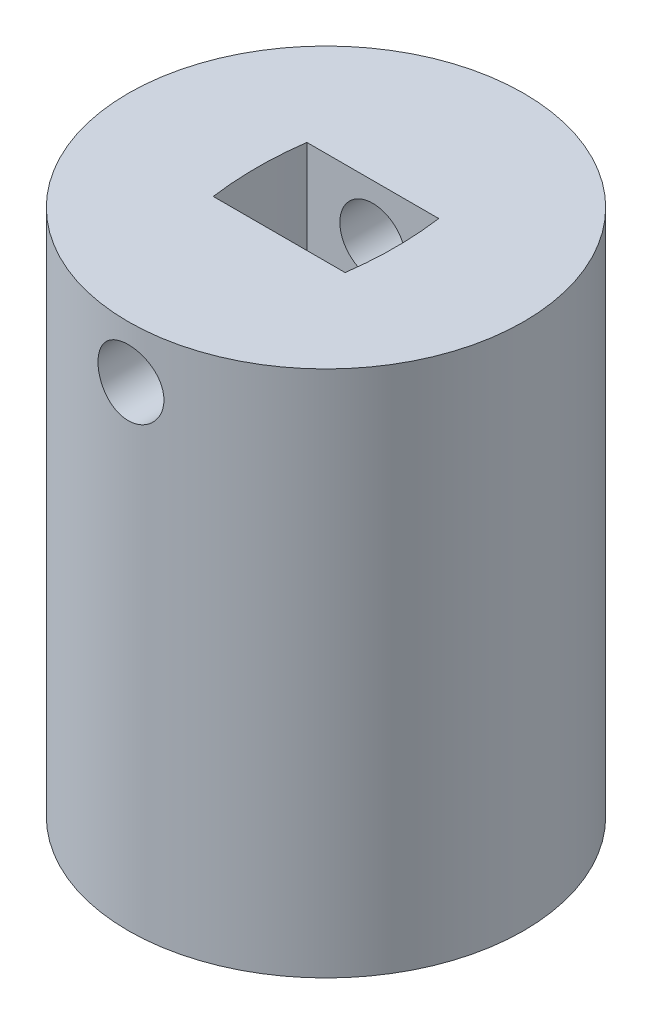
SolidWorks part; units mm, degrees
ref_plane "Front Plane" through (0, 0, 0) normal (0, 0, 1) x (1, 0, 0)
ref_plane "Top Plane" through (0, 0, 0) normal (0, 1, 0) x (1, 0, 0)
ref_plane "Right Plane" through (0, 0, 0) normal (1, 0, 0) x (0, 0, -1)
sketch "Sketch1" plane through (0, 0, 0) normal (0, 1, 0) x (1, 0, 0)
  circle A0 centre (0, 0) radius 15
  dimension "D1" = 30
extrude "Boss-Extrude1" add sketch "Sketch1" along normal blind 40
sketch "Sketch2" plane through (0, 0, 0) normal (0, -1, 0) x (1, 0, 0)
  line L0 (-4, 5) -> (4, 5)
  line L1 (-4, -5) -> (4, -5)
  spline S0 degree 2 poles (-4, 5) (-8.2, -0.0056) (-4, -5) knots 0 0 0 1 1 1
  spline S1 degree 2 poles (4, 5) (8.2, 0.0092) (4, -5) knots 0 0 0 1 1 1
  point P7 (5.4182, 0)
  point P8 (5.9111, 0)
  point P9 (-7.0321, 0)
  point P10 (3.93, 0)
  dimension "D2" = 0
  dimension "D1" = 10
  dimension "D3" = 5
  dimension "D4" = 12.2
  dimension "D5" = 8
  dimension "D6" = 6.1
extrude "Cut-Extrude1" cut sketch "Sketch2" against normal blind 15
sketch "Sketch3" plane through (0, 0, -5) normal (0, 0, 1) x (1, 0, 0)
  circle A0 centre (0, 12.0042) radius 2
  dimension "D1" = 4
extrude "Cut-Extrude2" cut sketch "Sketch3" against normal blind 15
sketch "Sketch4" plane through (0, 40, 0) normal (0, 1, 0) x (1, 0, 0)
  line L0 (-5, 3.55) -> (5, 3.55)
  line L1 (-5, -3.55) -> (5, -3.55)
  spline S0 degree 2 poles (-5, 3.55) (-5.4916, 0) (-5, -3.55) knots 0 0 0 1 1 1
  spline S1 degree 2 poles (5, 3.55) (5.4916, 0) (5, -3.55) knots 0 0 0 1 1 1
  dimension "D1" = 10
  dimension "D2" = 0
  dimension "D3" = 7.1
  dimension "D4" = 3.55
  dimension "D5" = 5
extrude "Cut-Extrude3" cut sketch "Sketch4" against normal blind 9
sketch "Sketch5" plane through (0, 0, 3.55) normal (0, 0, -1) x (-1, 0, 0)
  circle A0 centre (0, 36) radius 2.5
  point P6 (0, 0)
  dimension "D2" = 5
extrude "Cut-Extrude4" cut sketch "Sketch5" against normal through all both and the other way through all
